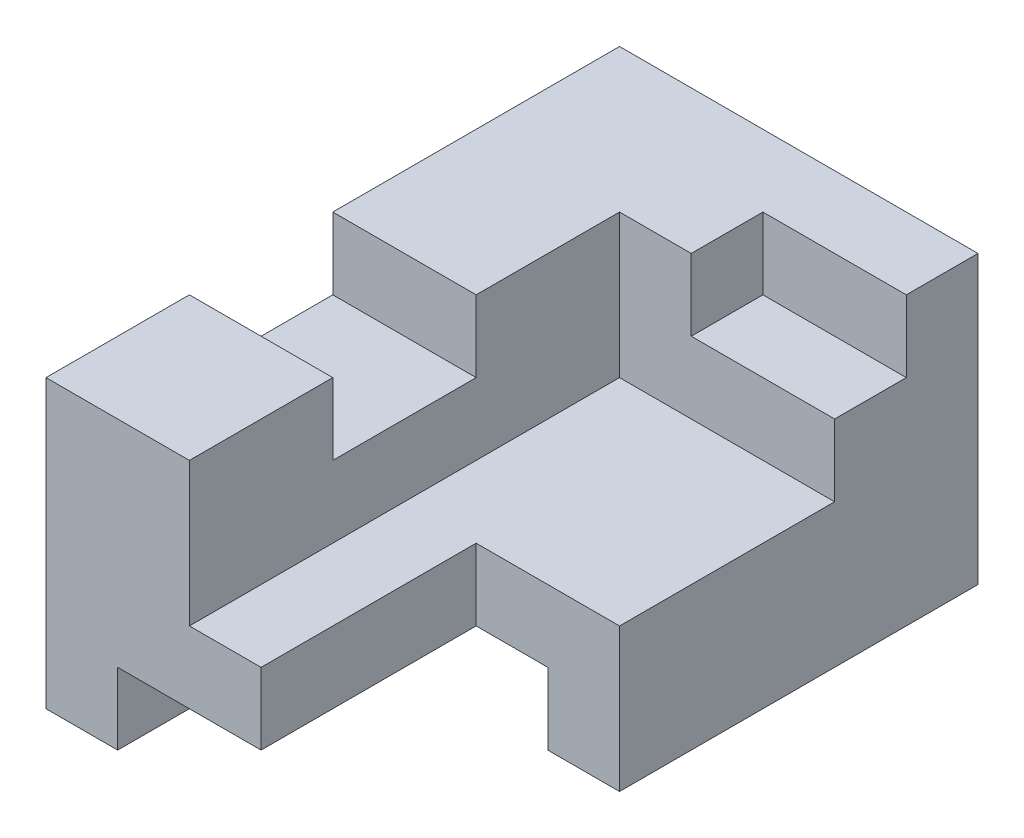
SolidWorks part; units mm, degrees
ref_plane "Front Plane" through (0, 0, 0) normal (0, 0, 1) x (1, 0, 0)
ref_plane "Top Plane" through (0, 0, 0) normal (0, 1, 0) x (1, 0, 0)
ref_plane "Right Plane" through (0, 0, 0) normal (1, 0, 0) x (0, 0, -1)
sketch "Sketch1" plane through (0, 0, 0) normal (0, 0, 1) x (1, 0, 0)
  line L1 (2.5, -2) -> (-2.5, -2)
  line L2 (2.5, -2) -> (2.5, 2)
  line L3 (2.5, 2) -> (-2.5, 2)
  line L4 (-2.5, -2) -> (-2.5, 2)
  line L5 (2.5, -2) -> (-2.5, 2) construction
  line L6 (2.5, 2) -> (-2.5, -2) construction
  point P0 (0, 0)
  dimension "D1" = 5
  dimension "D2" = 4
extrude "Boss-Extrude1" add sketch "Sketch1" along normal blind 8
sketch "Sketch2" plane through (0, 2, 0) normal (0, 1, 0) x (1, 0, 0)
  line L0 (-0.5, -4) -> (-2.5, -4)
  line L1 (-2.5, -8) -> (-2.5, 0) construction
  line L2 (-0.5, -4) -> (-0.5, -6)
  line L3 (-0.5, -6) -> (-2.5, -6)
  line L4 (-2.5, -6) -> (-2.5, -4)
  line L6 (2.5, -1) -> (0.5, -1)
  line L7 (2.5, -8) -> (2.5, 0) construction
  line L8 (0.5, -1) -> (0.5, -2)
  line L9 (0.5, -2) -> (2.5, -2)
  line L10 (2.5, -2) -> (2.5, -1)
  dimension "D1" = 4
  dimension "D2" = 2
  dimension "D3" = 2
  dimension "D4" = 2
  dimension "D5" = 1
  dimension "D6" = 1
extrude "Cut-Extrude1" cut sketch "Sketch2" against normal blind 1
sketch "Sketch4" plane through (2.5, 0, 0) normal (1, 0, 0) x (0, 0, -1)
  line L1 (-8.1128, 0) -> (-2, 0)
  line L2 (-8.1128, 0) -> (-8.1128, 2)
  line L3 (-8.1128, 2) -> (-2, 2)
  line L4 (-2, 0) -> (-2, 2)
  dimension "D1" = 2
extrude "Cut-Extrude2" cut sketch "Sketch4" against normal blind 3
sketch "Sketch5" plane through (0, 0, 0) normal (0, 1, 0) x (1, 0, 0)
  line L1 (2.5, -8) -> (0.5, -8)
  line L2 (2.5, -8) -> (2.5, -5)
  line L3 (2.5, -5) -> (0.5, -5)
  line L4 (0.5, -8) -> (0.5, -5)
  dimension "D1" = 2
  dimension "D2" = 3
extrude "Cut-Extrude3" cut sketch "Sketch5" against normal blind 3
sketch "Sketch6" plane through (0, 0, 8) normal (0, 0, 1) x (1, 0, 0)
  line L0 (-2.5, -2) -> (0.5, -2) construction
  line L1 (-1.5, -2) -> (1.5, -2)
  line L2 (-1.5, -2) -> (-1.5, -1)
  line L3 (-1.5, -1) -> (1.5, -1)
  line L4 (1.5, -2) -> (1.5, -1)
  line L5 (-2.5, 2) -> (-2.5, -2) construction
  line L6 (2.5, -2) -> (2.5, 0) construction
  dimension "D1" = 1
  dimension "D2" = 1
  dimension "D3" = 1
extrude "Cut-Extrude5" cut sketch "Sketch6" against normal through all
